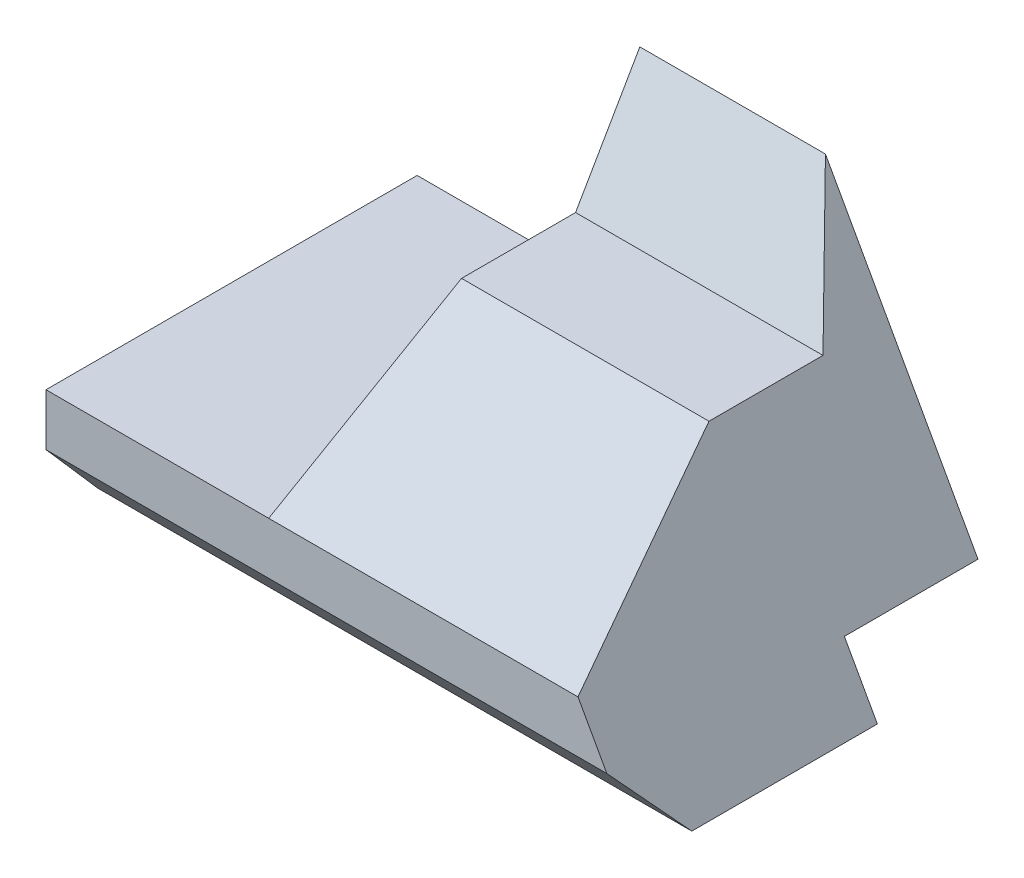
SolidWorks part; units mm, degrees
other "Markup1"
sketch "Sketch9" plane through (40, 0, 50) normal (0.9145, 0.0077, 0.4045) x (0.404, -0.0717, -0.9119)
material "Plain Carbon Steel"
ref_plane "Front Plane" through (0, 0, 0) normal (0, 0, 1) x (1, 0, 0)
ref_plane "Top Plane" through (0, 0, 0) normal (0, 1, 0) x (1, 0, 0)
ref_plane "Right Plane" through (0, 0, 0) normal (1, 0, 0) x (0, 0, -1)
sketch "Sketch8" plane through (0, 0, 0) normal (1, 0, 0) x (0, 0, -1)
  line L0 (0, -30) -> (-50, -30) construction
  line L2 (-50, -30) -> (-50, -37)
  line L3 (-43, -45) -> (-18, -45)
  line L4 (0, 0) -> (0, -37)
  line L5 (0, -37) -> (-50, -37) construction
  line L6 (0, -37) -> (-18, -37)
  line L9 (-18, -37) -> (-18, -45)
  line L10 (-43, -45) -> (-50, -37)
  line L11 (-50, -30) -> (-24.0192, -15)
  line L13 (0, 0) -> (-8.6603, -15)
  line L14 (-24.0192, -15) -> (-8.6603, -15)
  point P0 (0, 0)
  point P7 (-18, -45)
  point P8 (0, -37)
  point P12 (-43, -45)
  point P15 (0, -15)
  dimension "D1" = 45
  dimension "D2" = 8
  dimension "D3" = 15
  dimension "D4" = 32
  dimension "D5" = 7
  dimension "D6" = 50
  dimension "D7" = 15
  dimension "D8" = 30
  dimension "D9" = 30
  dimension "D10" = 15
extrude "Boss-Extrude3" add sketch "Sketch8" along normal mid plane 80
ref_plane "Plane1" through (0, 0, 50) normal (0, 0, 1) x (1, 0, 0)
sketch "Sketch10" plane through (0, 0, 50) normal (0, 0, 1) x (1, 0, 0)
  line L0 (-40, 0) -> (-40, -15) construction
  line L2 (40, -15) -> (40, 0) construction
  line L3 (40, 0) -> (-40, 0) construction
  line L4 (-40, -15) -> (-40, -30) construction
  line L5 (-40, -30) -> (40, -30) construction
  line L6 (40, -30) -> (40, -15) construction
  line L8 (-40, 0) -> (-40, -15)
  line L10 (40, -15) -> (40, 0)
  line L11 (40, 0) -> (-40, 0)
  line L12 (-40, -15) -> (-40, -30)
  line L13 (-40, -30) -> (40, -30)
  line L14 (40, -30) -> (40, -15)
  line L16 (-10, 0) -> (-10, -30)
  dimension "D1" = 30
extrude "Cut-Extrude1" cut sketch "Sketch10" against normal through all contours L16 L11 L8 L12 L13
sketch "Sketch11" plane through (0, 0, 50) normal (0, 0, 1) x (1, 0, 0)
  line L0 (-10, 0) -> (-10, -15) construction
  line L1 (-10, -15) -> (40, -15) construction
  line L2 (40, -15) -> (40, 0) construction
  line L3 (40, 0) -> (-10, 0) construction
  line L4 (-10, -15) -> (-10, -30) construction
  line L5 (40, -30) -> (40, -15) construction
  line L6 (40, -15) -> (-10, -15) construction
  line L7 (-40, -30) -> (-40, -37) construction
  line L8 (40, -37) -> (40, -30) construction
  line L9 (-10, -30) -> (-40, -30) construction
  line L10 (-40, -37) -> (-40, -45) construction
  line L11 (-40, -45) -> (40, -45) construction
  line L12 (40, -45) -> (40, -37) construction
  line L13 (-10, 0) -> (-10, -15)
  line L14 (-10, -15) -> (40, -15)
  line L15 (40, -15) -> (40, 0)
  line L16 (40, 0) -> (-10, 0)
  line L17 (-10, -15) -> (-10, -30)
  line L18 (40, -30) -> (40, -15)
  line L19 (40, -15) -> (-10, -15)
  line L20 (-40, -30) -> (-40, -37)
  line L21 (40, -37) -> (40, -30)
  line L22 (-10, -30) -> (-40, -30)
  line L23 (-40, -37) -> (-40, -45)
  line L24 (-40, -45) -> (40, -45)
  line L25 (40, -45) -> (40, -37)
  line L26 (40, -45) -> (15, 0)
  dimension "D1" = 25
extrude "Cut-Extrude3" cut sketch "Sketch11" against normal through all contours L26 L19 L15 L16 | L26 L25 L21 L18 L19
